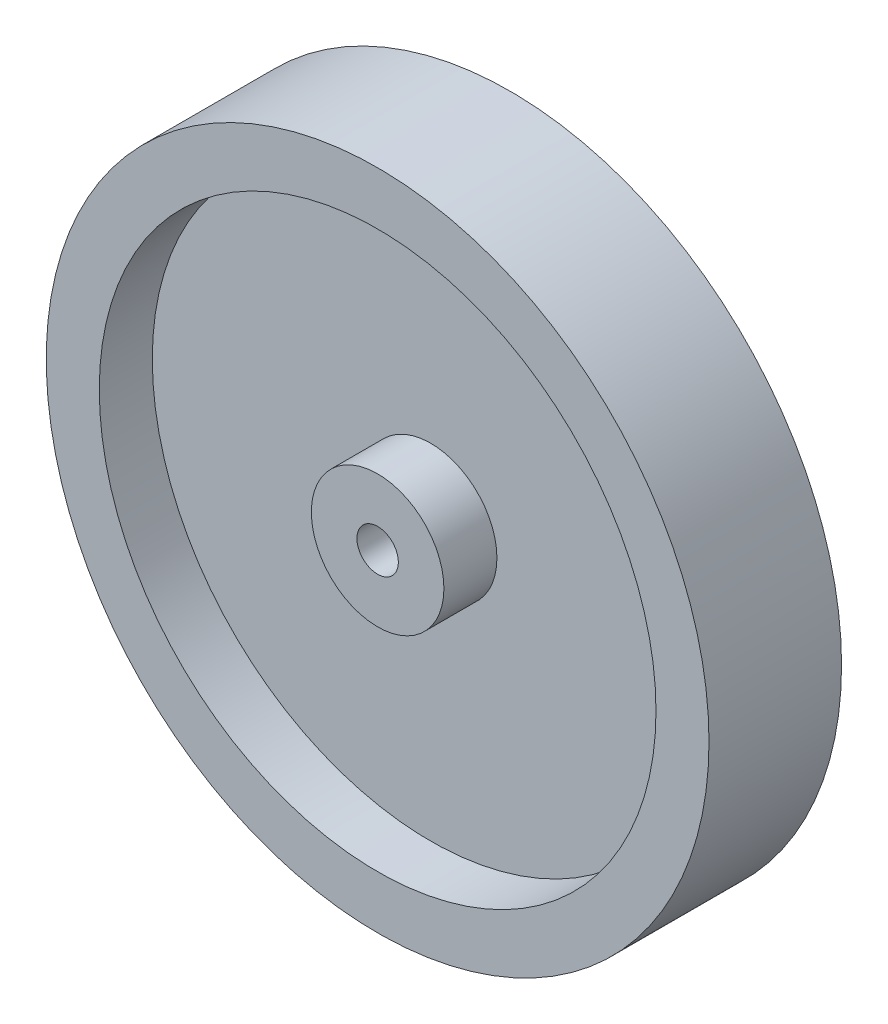
SolidWorks part; units mm, degrees
material "PP Copolymer"
ref_plane "Front Plane" through (0, 0, 0) normal (0, 0, 1) x (1, 0, 0)
ref_plane "Top Plane" through (0, 0, 0) normal (0, 1, 0) x (1, 0, 0)
ref_plane "Right Plane" through (0, 0, 0) normal (1, 0, 0) x (0, 0, -1)
sketch "Sketch1" plane through (0, 0, 0) normal (0, 0, 1) x (1, 0, 0)
  circle A0 centre (0, 0) radius 63.5
  circle A1 centre (0, 0) radius 3.9688
  dimension "D1" = 127
  dimension "D2" = 7.9375
extrude "Boss-Extrude1" add sketch "Sketch1" against normal mid plane 25.4
sketch "Sketch2" plane through (0, 0, 12.7) normal (0, 0, 1) x (1, 0, 0)
  circle A0 centre (0, 0) radius 12.7
  circle A1 centre (0, 0) radius 53.34
  dimension "D1" = 106.68
  dimension "D2" = 25.4
extrude "Cut-Extrude1" cut sketch "Sketch2" against normal blind 10.16
mirror "Mirror1" about plane through (0, 0, 0) normal (0, 0, 1) of "Cut-Extrude1"
